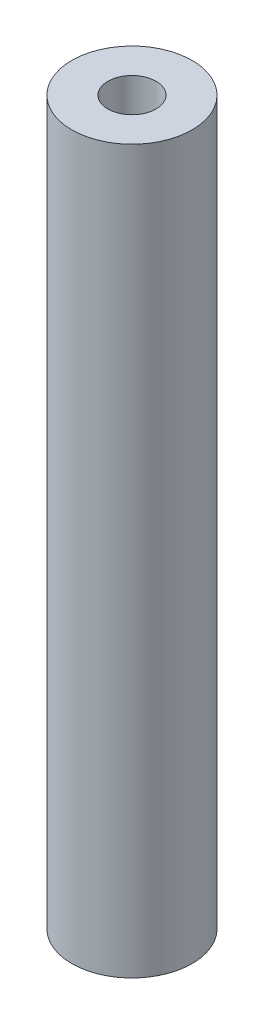
SolidWorks part; units mm, degrees
material "6061-T6 (SS)"
ref_plane "Front Plane" through (0, 0, 0) normal (0, 0, 1) x (1, 0, 0)
ref_plane "Top Plane" through (0, 0, 0) normal (0, 1, 0) x (1, 0, 0)
ref_plane "Right Plane" through (0, 0, 0) normal (1, 0, 0) x (0, 0, -1)
sketch "Sketch1" plane through (0, 0, 0) normal (0, 1, 0) x (1, 0, 0)
  circle A0 centre (0, 0) radius 2.5
  circle A1 centre (0, 0) radius 1
  dimension "D1" = 5
extrude "Boss-Extrude1" add sketch "Sketch1" along normal blind 30
